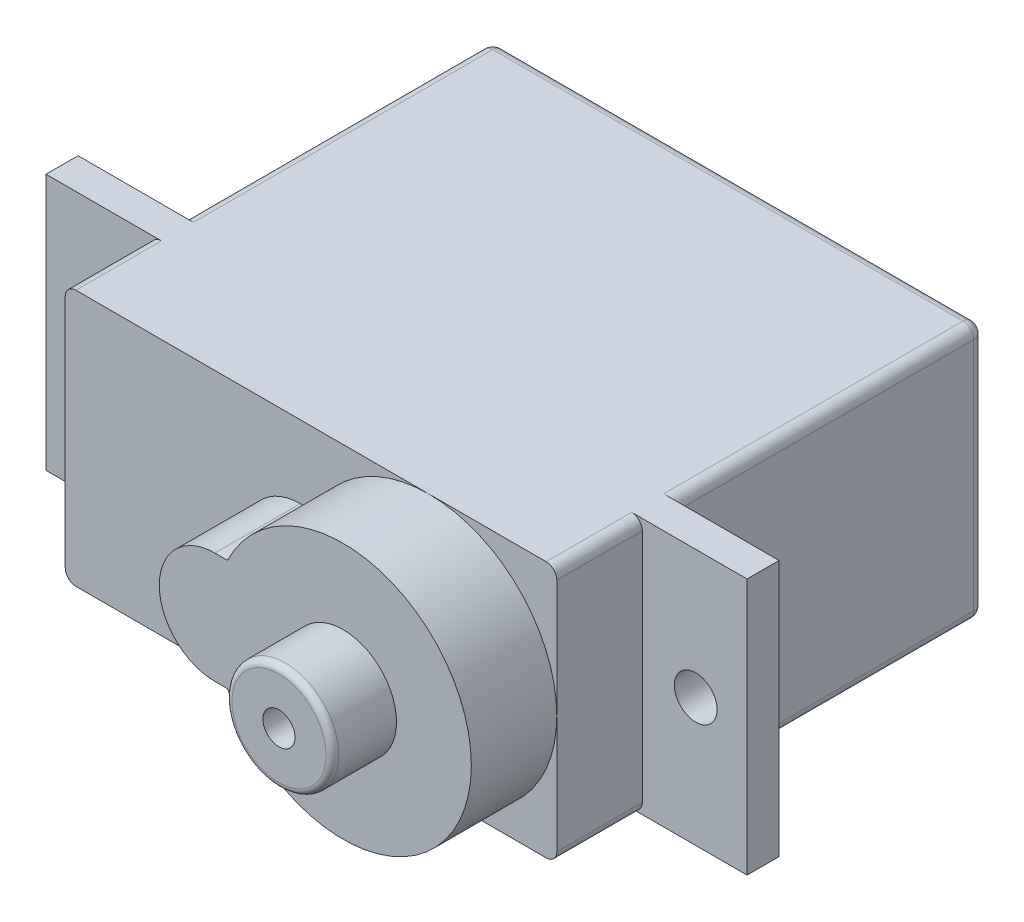
SolidWorks part; units mm, degrees
ref_plane "前视基准面" through (0, 0, 0) normal (0, 0, 1) x (1, 0, 0)
ref_plane "上视基准面" through (0, 0, 0) normal (0, 1, 0) x (1, 0, 0)
ref_plane "右视基准面" through (0, 0, 0) normal (1, 0, 0) x (0, 0, -1)
sketch "草图1" plane through (0, 0, 0) normal (0, 0, 1) x (1, 0, 0)
  line L1 (-16.4, 6) -> (16.4, 6)
  line L2 (-16.4, 6) -> (-16.4, -6)
  line L3 (-16.4, -6) -> (16.4, -6)
  line L4 (16.4, 6) -> (16.4, -6)
  dimension "D1" = 32.8
  dimension "D2" = 16.4
  dimension "D3" = 12
  dimension "D4" = 6
extrude "凸台-拉伸1" add sketch "草图1" along normal blind 1.5
sketch "草图2" plane through (0, 0, 1.5) normal (0, 0, 1) x (1, 0, 0)
  line L0 (16.4, 6) -> (-16.4, 6) construction
  line L1 (-11.5, 6) -> (11.5, 6)
  line L2 (-11.5, 6) -> (-11.5, -6)
  line L3 (-11.5, -6) -> (11.5, -6)
  line L4 (11.5, 6) -> (11.5, -6)
  line L5 (-16.4, -6) -> (16.4, -6) construction
  line L10 (16.4, -6) -> (16.4, 6) construction
  dimension "D1" = 23
  dimension "D2" = 4.9
extrude "凸台-拉伸2" add sketch "草图2" along normal blind 4
sketch "草图3" plane through (0, 0, 5.5) normal (0, 0, 1) x (1, 0, 0)
  line L1 (11.5, -6) -> (11.5, 6) construction
  line L2 (-11.5, 6) -> (-11.5, -6) construction
  line L3 (-0.5, 2.6) -> (0.0926, 2.6)
  line L4 (-0.5, -2.6) -> (0.0926, -2.6)
  arc A0 (0.0926, -2.6) -> (0.0926, 2.6) centre (5.5, 0) ccw
  arc A1 (-0.5, 2.6) -> (-0.5, -2.6) centre (-0.5, 0) ccw
  dimension "D1" = 12
  dimension "D3" = 5.2
  dimension "D4" = 11
  dimension "D2" = 6
sketch "草图6" plane through (0, 0, 0) normal (0, 0, -1) x (-1, 0, 0)
  line L0 (-16.4, 6) -> (16.4, 6) construction
  line L1 (-11.5, 6) -> (11.5, 6)
  line L2 (-11.5, 6) -> (-11.5, -6)
  line L3 (-11.5, -6) -> (11.5, -6)
  line L4 (11.5, 6) -> (11.5, -6)
  line L5 (16.4, -6) -> (-16.4, -6) construction
  line L8 (16.4, 6) -> (16.4, -6) construction
  dimension "D1" = 23
  dimension "D2" = 4.9
extrude "凸台-拉伸5" add sketch "草图6" along normal blind 14.5
sketch "草图7" plane through (0, 0, 1.5) normal (0, 0, 1) x (1, 0, 0)
  line L0 (-16.4, 6) -> (-16.4, -6) construction
  line L1 (16.4, -6) -> (16.4, 6) construction
  circle A0 centre (-14, 0) radius 1
  circle A1 centre (14, 0) radius 1
  dimension "D1" = 2
  dimension "D2" = 2
  dimension "D3" = 28
  dimension "D4" = 2.4
  dimension "D5" = 2.4
extrude "切除-拉伸2" cut sketch "草图7" against normal blind 2
extrude "凸台-拉伸6" add sketch "草图3" along normal blind 4
sketch "草图8" plane through (0, 0, 9.5) normal (0, 0, 1) x (1, 0, 0)
  circle A0 centre (5.5, 0) radius 2.5
  dimension "D1" = 5
extrude "凸台-拉伸7" add sketch "草图8" along normal blind 3
fillet "圆角1" radius 0.3 1 edges at (8, 0, 12.5)
sketch "草图9" plane through (0, 0, 12.5) normal (0, 0, 1) x (1, 0, 0)
  circle A0 centre (5.5, 0) radius 0.75
  dimension "D1" = 1.5
extrude "切除-拉伸3" cut sketch "草图9" against normal blind 5
fillet "圆角2" radius 0.5 12 edges at (0, -6, -14.5) (-11.5, 0, -14.5) (0, 6, -14.5) (11.5, 0, -14.5)
